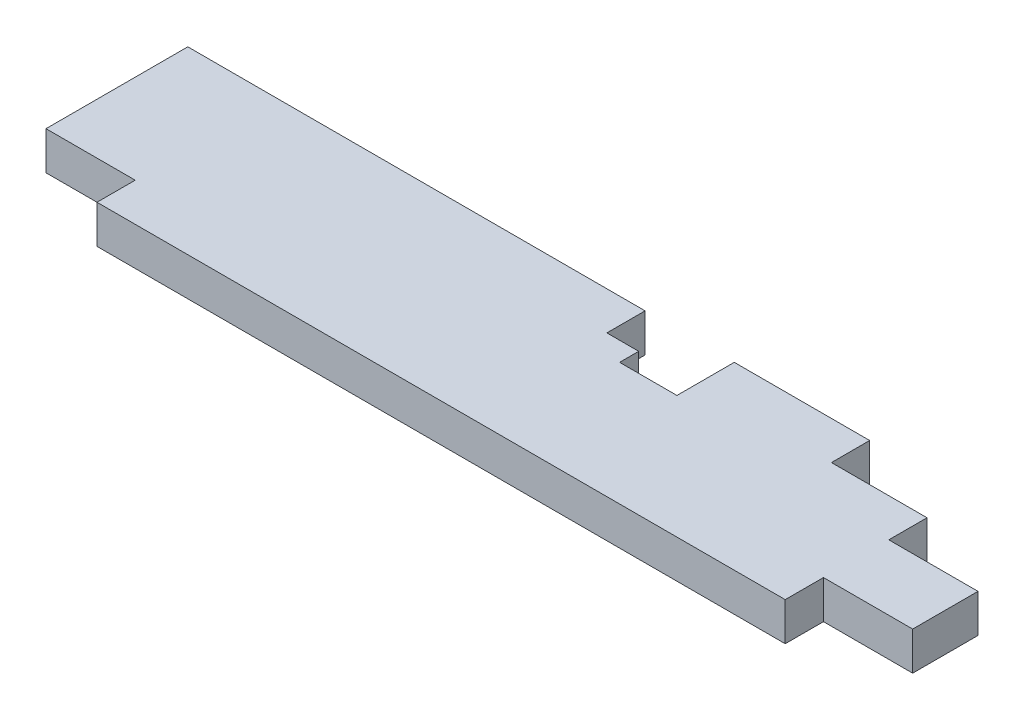
SolidWorks part; units mm, degrees
material "Pine"
ref_plane "Front Plane" through (0, 0, 0) normal (0, 0, 1) x (1, 0, 0)
ref_plane "Top Plane" through (0, 0, 0) normal (0, 1, 0) x (1, 0, 0)
ref_plane "Right Plane" through (0, 0, 0) normal (1, 0, 0) x (0, 0, -1)
sketch "Sketch1" plane through (0, 0, 0) normal (0, 1, 0) x (1, 0, 0)
  line L1 (0, 0) -> (863.6, 0)
  line L2 (0, 0) -> (0, 179.3875)
  line L3 (0, 179.3875) -> (863.6, 179.3875)
  line L4 (863.6, 0) -> (863.6, 179.3875)
  dimension "D1" = 179.3875
  dimension "D2" = 863.6
extrude "Boss-Extrude1" add sketch "Sketch1" along normal blind 38.1
sketch "Sketch2" plane through (0, 0, 0) normal (0, -1, 0) x (1, 0, 0)
  line L1 (863.6, -38.1) -> (774.7, -38.1)
  line L2 (863.6, 0) -> (863.6, -38.1)
  line L4 (774.7, 0) -> (774.7, -38.1)
  line L5 (0, -179.3875) -> (0, 0) construction
  line L6 (774.7, 0) -> (863.6, 0)
  line L7 (863.6, 0) -> (863.6, -179.3875) construction
  line L8 (0, 0) -> (863.6, 0) construction
  dimension "D1" = 774.7
  dimension "D2" = 38.1
  dimension "D3" = 863.6
extrude "Cut-Extrude4" cut sketch "Sketch2" against normal through all
sketch "Sketch3" plane through (0, 0, 0) normal (0, -1, 0) x (1, 0, 0)
  line L1 (863.6, -179.3875) -> (679.45, -179.3875)
  line L2 (863.6, -179.3875) -> (863.6, -141.2875)
  line L3 (863.6, -141.2875) -> (679.45, -141.2875)
  line L4 (679.45, -179.3875) -> (679.45, -141.2875)
  line L5 (863.6, -179.3875) -> (0, -179.3875) construction
  line L6 (863.6, -38.1) -> (863.6, -179.3875) construction
  dimension "D1" = 141.2875
  dimension "D2" = 679.45
extrude "Cut-Extrude1" cut sketch "Sketch3" against normal through all
sketch "Sketch4" plane through (0, 0, 0) normal (0, -1, 0) x (1, 0, 0)
  line L0 (544.5645, -122.2375) -> (544.5645, -179.3875)
  line L1 (544.5645, -179.3875) -> (455.676, -179.3875)
  line L3 (487.426, -141.2875) -> (455.676, -141.2875)
  line L4 (455.676, -179.3875) -> (455.676, -141.2875)
  line L5 (544.5645, -122.2375) -> (487.426, -122.2375)
  line L8 (487.426, -122.2375) -> (487.426, -141.2875)
  line L10 (679.45, -179.3875) -> (0, -179.3875) construction
  line M8 (0, -179.3875) -> (679.45, -179.3875)
  dimension "D1" = 122.2375
  dimension "D2" = 455.676
  dimension "D3" = 88.8885
  dimension "D4" = 141.2875
  dimension "D5" = 487.426
extrude "Cut-Extrude2" cut sketch "Sketch4" against normal through all contours L5 L8 L3 L4 L0 M8
sketch "Sketch5" plane through (0, 0, 0) normal (0, -1, 0) x (1, 0, 0)
  line L0 (863.6, -38.1) -> (863.6, -141.2875) construction
  line L1 (863.6, -141.2875) -> (774.7, -141.2875)
  line L2 (863.6, -141.2875) -> (863.6, -103.1875)
  line L3 (863.6, -103.1875) -> (774.7, -103.1875)
  line L4 (774.7, -141.2875) -> (774.7, -103.1875)
  line L5 (863.6, -141.2875) -> (679.45, -141.2875) construction
  point P9 (819.15, -141.2875)
  dimension "D1" = 103.1875
  dimension "D2" = 774.7
extrude "Cut-Extrude3" cut sketch "Sketch5" against normal through all
sketch "Sketch6" plane through (0, 38.1, 0) normal (0, 1, 0) x (1, 0, 0)
  line L1 (0, 0) -> (88.9, 0)
  line L2 (0, 0) -> (0, 38.1)
  line L3 (0, 38.1) -> (88.9, 38.1)
  line L4 (88.9, 0) -> (88.9, 38.1)
  dimension "D1" = 88.9
  dimension "D2" = 38.1
extrude "Cut-Extrude5" cut sketch "Sketch6" against normal through all
